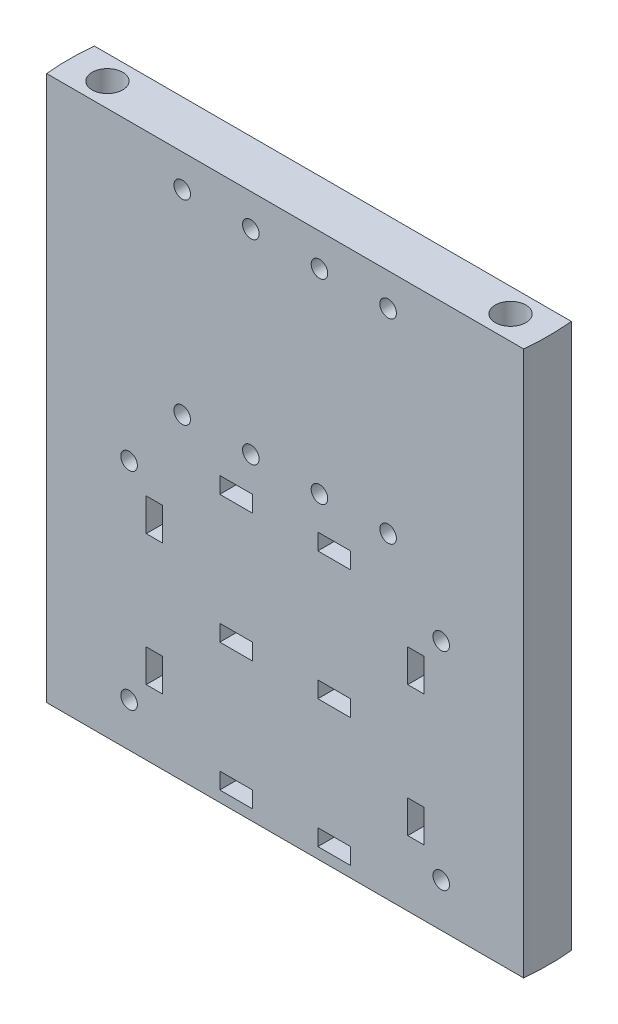
SolidWorks part; units mm, degrees
ref_plane "Front Plane" through (0, 0, 0) normal (0, 0, 1) x (1, 0, 0)
ref_plane "Top Plane" through (0, 0, 0) normal (0, 1, 0) x (1, 0, 0)
ref_plane "Right Plane" through (0, 0, 0) normal (1, 0, 0) x (0, 0, -1)
sketch "Sketch1" plane through (0, 0, 0) normal (0, 1, 0) x (1, 0, 0)
  line L0 (-60.706, 5.5591) -> (60.706, 5.5591)
  line L1 (-60.706, -5.5591) -> (60.706, -5.5591)
  arc A0 (60.706, -5.5591) -> (60.706, 5.5591) centre (0, 0) ccw
  arc A1 (-60.706, 5.5591) -> (-60.706, -5.5591) centre (0, 0) ccw
  point P1 (0, 5.5591)
  dimension "D1" = 121.92
  dimension "D4" = 60.96
  dimension "D2" = 121.412
  dimension "D3" = 121.412
  dimension "D5" = 5.5591
extrude "Boss-Extrude1" add sketch "Sketch1" along normal blind 127
sketch "Sketch2" plane through (0, 0, 0) normal (0, 1, 0) x (1, 0, 0)
  circle A0 centre (0, 0) radius 61.595
  dimension "D1" = 123.19
sketch "Sketch3" plane through (0, 0, 0) normal (0, 1, 0) x (1, 0, 0)
  circle A0 centre (0, 0) radius 63.5
  dimension "D1" = 127
ref_plane "Raft Top" through (0, 0, 9.9465) normal (0, 0, -1) x (-1, 0, 0)
sketch "Sketch10" plane through (0, 0, -5.5591) normal (0, 0, -1) x (-1, 0, 0)
  line L0 (-32.385, 2.54) -> (-32.385, 66.04)
  line L5 (-32.385, 66.04) -> (32.385, 66.04)
  line L10 (32.385, 66.04) -> (32.385, 2.54)
  line L11 (32.385, 2.54) -> (-32.385, 2.54)
  line L16 (60.706, 127) -> (60.706, 0) construction
  line L17 (61.595, 0) -> (-61.595, 0) construction
  line L18 (-60.706, 127) -> (-60.706, 0) construction
  dimension "D1" = 28.321
  dimension "D2" = 2.54
  dimension "D3" = 28.321
  dimension "D4" = 63.5
  dimension "D5" = 64.77
sketch "Sketch13" plane through (0, 127, 0) normal (0, 1, 0) x (1, 0, 0)
  line L2 (60.706, 5.5591) -> (-60.706, 5.5591)
  line L3 (-60.706, -5.5591) -> (60.706, -5.5591)
  line L4 (60.706, 5.5591) -> (-60.706, 5.5591)
  line L5 (-60.706, -5.5591) -> (60.706, -5.5591)
  line L6 (-46.99, 5.5591) -> (-46.99, -5.5591) construction
  line L7 (0, -55) -> (0, 55) construction
  line L8 (-32.385, 5.5591) -> (32.385, 5.5591) construction
  arc A2 (-60.706, 5.5591) -> (-60.706, -5.5591) centre (0, 0) ccw
  arc A3 (60.706, -5.5591) -> (60.706, 5.5591) centre (0, 0) ccw
  arc A4 (-60.706, 5.5591) -> (-60.706, -5.5591) centre (0, 0) ccw
  arc A5 (60.706, -5.5591) -> (60.706, 5.5591) centre (0, 0) ccw
  point P10 (-46.99, 0)
  point P13 (46.99, 0)
  dimension "D2" = 46.99
  dimension "D1" = 0
hole_wizard "1/4 Clearance Hole1" positions "Sketch14" profile "Sketch15" hole size "1/4" standard "ANSI Inch" end condition through all
sketch "Sketch14" plane through (0, 127, 0) normal (0, 1, 0) x (1, 0, 0)
  point P0 (-46.99, 0)
  point P3 (46.99, 0)
sketch "Sketch15" plane through (-46.99, 127, 0) normal (1, 0, 0) x (0, 0, 1)
  line L0 (0, 0) -> (0, 127)
  line L1 (0, 127) -> (3.5712, 127)
  line L2 (3.5712, 127) -> (3.5712, 0)
  line L5 (3.5712, 0) -> (0, 0)
  line L11 (0, -6.35) -> (0, 107.95) construction
  dimension "Thru Hole Dia." = 7.1425
  dimension "Thru Hole Depth" = 127
sketch "Sketch16" plane through (0, 0, 9.9465) normal (0, 0, -1) x (-1, 0, 0)
  line L0 (60.706, 127) -> (-60.706, 127) construction
  line L3 (0, 55) -> (0, -55) construction
  point P0 (-24.003, 119.38)
  point P1 (-8.001, 119.38)
  point P2 (-8.001, 73.914)
  point P3 (-24.003, 73.914)
  point P28 (8.001, 73.914)
  point P29 (24.003, 73.914)
  point P30 (8.001, 119.38)
  point P31 (24.003, 119.38)
  dimension "D1" = 16.002
  dimension "D2" = 45.466
  dimension "D3" = 8.001
  dimension "D4" = 7.62
sketch "Sketch19" plane through (0, 0, -5.5591) normal (0, 0, -1) x (-1, 0, 0)
  line L0 (0, 66.04) -> (0, 2.54) construction
  line L3 (-32.385, 34.29) -> (32.385, 34.29) construction
  line L8 (-15.24, 36.195) -> (-7.62, 36.195)
  line L9 (-15.24, 36.195) -> (-15.24, 32.385)
  line L10 (-15.24, 32.385) -> (-7.62, 32.385)
  line L11 (-7.62, 36.195) -> (-7.62, 32.385)
  line L19 (32.385, 45.72) -> (28.575, 45.72)
  line L20 (-15.24, 66.04) -> (-7.62, 66.04)
  line L21 (-15.24, 66.04) -> (-15.24, 62.23)
  line L22 (-15.24, 62.23) -> (-7.62, 62.23)
  line L23 (-7.62, 66.04) -> (-7.62, 62.23)
  line L36 (15.24, 62.23) -> (7.62, 62.23)
  line L37 (7.62, 66.04) -> (7.62, 62.23)
  line L38 (15.24, 66.04) -> (7.62, 66.04)
  line L39 (15.24, 66.04) -> (15.24, 62.23)
  line L40 (-15.24, 6.35) -> (-7.62, 6.35)
  line L41 (-7.62, 2.54) -> (-7.62, 6.35)
  line L42 (-15.24, 2.54) -> (-7.62, 2.54)
  line L43 (-15.24, 2.54) -> (-15.24, 6.35)
  line L44 (15.24, 2.54) -> (15.24, 6.35)
  line L45 (15.24, 2.54) -> (7.62, 2.54)
  line L46 (7.62, 2.54) -> (7.62, 6.35)
  line L47 (15.24, 6.35) -> (7.62, 6.35)
  line L48 (-32.385, 53.34) -> (-28.575, 53.34)
  line L49 (-32.385, 53.34) -> (-32.385, 45.72)
  line L50 (-32.385, 45.72) -> (-28.575, 45.72)
  line L51 (-28.575, 53.34) -> (-28.575, 45.72)
  line L52 (28.575, 53.34) -> (28.575, 45.72)
  line L53 (32.385, 53.34) -> (28.575, 53.34)
  line L54 (32.385, 53.34) -> (32.385, 45.72)
  line L55 (32.385, 15.24) -> (32.385, 22.86)
  line L56 (32.385, 15.24) -> (28.575, 15.24)
  line L57 (28.575, 15.24) -> (28.575, 22.86)
  line L58 (32.385, 22.86) -> (28.575, 22.86)
  line L59 (-32.385, 22.86) -> (-28.575, 22.86)
  line L60 (-28.575, 15.24) -> (-28.575, 22.86)
  line L61 (-32.385, 15.24) -> (-28.575, 15.24)
  line L62 (-32.385, 15.24) -> (-32.385, 22.86)
  line L63 (-32.385, 66.04) -> (32.385, 66.04) construction
  line L64 (32.385, 66.04) -> (32.385, 2.54) construction
  line L65 (32.385, 2.54) -> (-32.385, 2.54) construction
  line L66 (-32.385, 2.54) -> (-32.385, 66.04) construction
  line L67 (7.62, 36.195) -> (7.62, 32.385)
  line L68 (15.24, 32.385) -> (7.62, 32.385)
  line L69 (15.24, 36.195) -> (15.24, 32.385)
  line L70 (15.24, 36.195) -> (7.62, 36.195)
  point P10 (0, 34.29)
  point P12 (-15.24, 36.195)
  point P22 (-15.24, 66.04)
  point P41 (-32.385, 53.34)
  dimension "D1" = 7.62
  dimension "D2" = 3.81
  dimension "D3" = 15.24
  dimension "D4" = 1.905
  dimension "D5" = 15.24
  dimension "D6" = 7.62
  dimension "D7" = 3.81
  dimension "D8" = 19.05
  dimension "D9" = 3.81
  dimension "D10" = 7.62
hole_wizard "#8 Clearance Hole1" positions "Sketch20" profile "Sketch21" hole size "#8" standard "ANSI Inch" end condition through all
sketch "Sketch20" plane through (0, 0, -5.5591) normal (0, 0, -1) x (-1, 0, 0)
  point P3 (-8.001, 119.38)
  point P9 (-8.001, 73.914)
  point P12 (8.001, 73.914)
  point P21 (8.001, 119.38)
sketch "Sketch21" plane through (8.001, 119.38, -5.5591) normal (1, 0, 0) x (0, 1, 0)
  line L0 (0, 0) -> (0, 11.1181)
  line L1 (0, 11.1181) -> (1.9304, 11.1181)
  line L2 (1.9304, 11.1181) -> (1.9304, 0)
  line L5 (1.9304, 0) -> (0, 0)
  line L11 (0, -6.35) -> (0, 107.95) construction
  dimension "Thru Hole Dia." = 3.8608
  dimension "Thru Hole Depth" = 11.1181
extrude "Cut-Extrude3" cut sketch "Sketch19" against normal through all
hole_wizard "#8 Clearance Hole2" positions "Sketch22" profile "Sketch24" hole size "#8" standard "ANSI Inch" end condition through all
sketch "Sketch22" plane through (0, 0, -5.5591) normal (0, 0, -1) x (-1, 0, 0)
  point P0 (-24.003, 119.38)
  point P3 (-24.003, 73.914)
  point P6 (24.003, 73.914)
  point P9 (24.003, 119.38)
sketch "Sketch24" plane through (24.003, 119.38, -5.5591) normal (1, 0, 0) x (0, 1, 0)
  line L0 (0, 0) -> (0, 11.1181)
  line L1 (0, 11.1181) -> (1.9304, 11.1181)
  line L2 (1.9304, 11.1181) -> (1.9304, 0)
  line L5 (1.9304, 0) -> (0, 0)
  line L11 (0, -6.35) -> (0, 107.95) construction
  dimension "Thru Hole Dia." = 3.8608
  dimension "Thru Hole Depth" = 11.1181
sketch "Sketch29" plane through (0, 0, -5.5591) normal (0, 0, -1) x (-1, 0, 0)
  line L0 (60.706, 127) -> (60.706, 0) construction
  line L1 (-40.386, 66.04) -> (40.386, 66.04)
  line L2 (-40.386, 66.04) -> (-40.386, 2.54)
  line L3 (-40.386, 2.54) -> (40.386, 2.54)
  line L4 (40.386, 66.04) -> (40.386, 2.54)
  line L5 (-60.706, 127) -> (-60.706, 0) construction
  line L6 (61.595, 0) -> (-61.595, 0) construction
  line L7 (-40.386, 34.29) -> (40.386, 34.29) construction
  line L10 (32.385, 53.34) -> (40.386, 53.34) construction
  line L12 (32.385, 66.04) -> (32.385, 2.54) construction
  line L13 (0, 69.85) -> (0, -69.85) construction
  point P8 (36.3855, 58.42)
  point P20 (36.3855, 53.34)
  point P24 (36.3855, 10.16)
  point P28 (-36.3855, 58.42)
  point P30 (-36.3855, 10.16)
  dimension "D1" = 20.32
  dimension "D2" = 20.32
  dimension "D3" = 2.54
  dimension "D4" = 63.5
  dimension "D5" = 80.772
  dimension "D6" = 7.62
  dimension "D7" = 12.7
hole_wizard "#8 Clearance Hole3" positions "Sketch34" profile "Sketch35" hole size "#8" standard "ANSI Inch" end condition through all
sketch "Sketch34" plane through (0, 0, -5.5591) normal (0, 0, -1) x (-1, 0, 0)
  point P0 (-36.3855, 58.42)
  point P3 (-36.3855, 10.16)
  point P6 (36.3855, 10.16)
  point P9 (36.3855, 58.42)
sketch "Sketch35" plane through (36.3855, 58.42, -5.5591) normal (1, 0, 0) x (0, 1, 0)
  line L0 (0, 0) -> (0, 11.1181)
  line L1 (0, 11.1181) -> (1.9304, 11.1181)
  line L2 (1.9304, 11.1181) -> (1.9304, 0)
  line L5 (1.9304, 0) -> (0, 0)
  line L11 (0, -6.35) -> (0, 107.95) construction
  dimension "Thru Hole Dia." = 3.8608
  dimension "Thru Hole Depth" = 11.1181
extrude "Cut-Extrude4" cut sketch "Sketch10" against normal blind 5.08
sketch "Sketch36" plane through (0, 127, 0) normal (0, 1, 0) x (1, 0, 0)
  circle A0 centre (0, 0) radius 55.88
  circle A1 centre (0, 0) radius 76.2
  dimension "D1" = 152.4
  dimension "D2" = 111.76
extrude "Cut-Extrude5" cut sketch "Sketch36" against normal through all
sketch "Sketch37" plane through (0, 0, -5.5591) normal (0, 0, -1) x (-1, 0, 0)
  line L1 (-40.386, 66.04) -> (40.386, 66.04)
  line L2 (-40.386, 66.04) -> (-40.386, 2.54)
  line L3 (-40.386, 2.54) -> (40.386, 2.54)
  line L4 (40.386, 66.04) -> (40.386, 2.54)
extrude "Cut-Extrude6" cut sketch "Sketch37" against normal up to surface (5.08 mm away) up to face at (11.43, 34.29, -0.4791)
